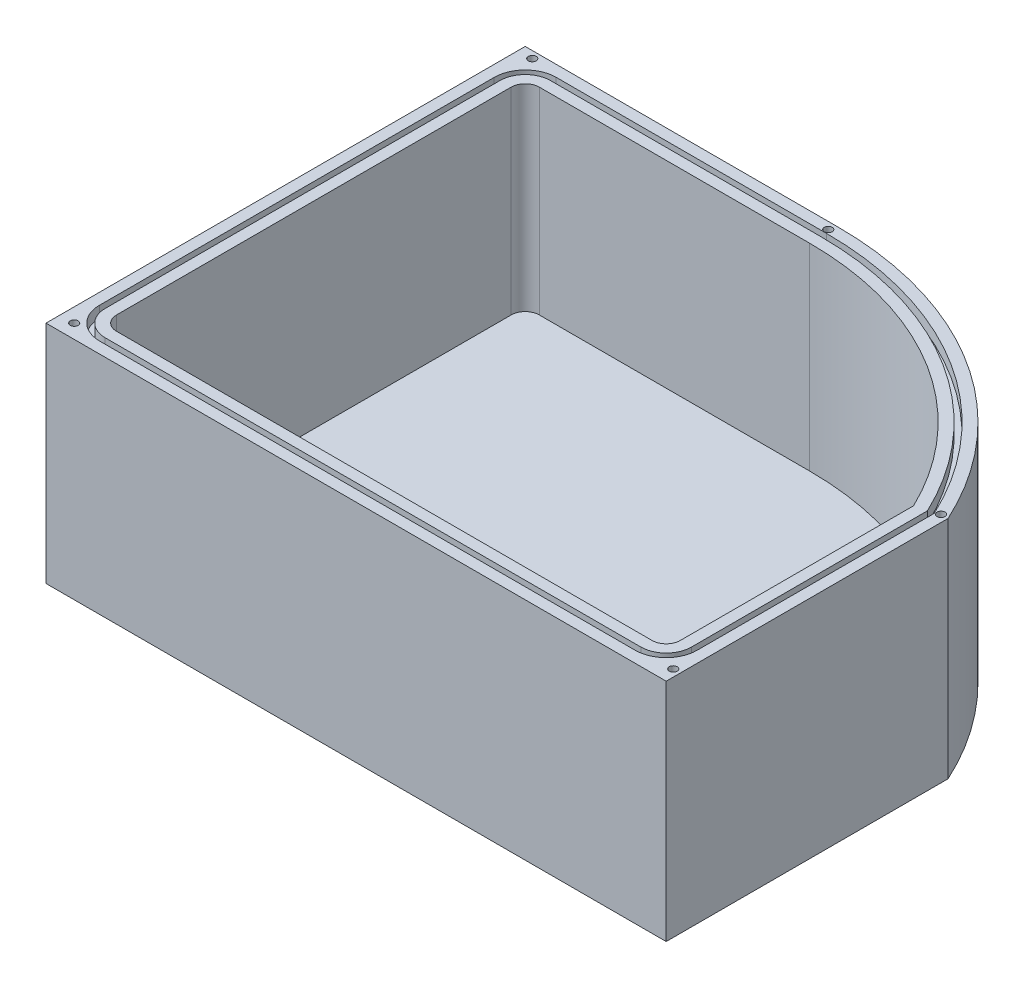
SolidWorks part; units mm, degrees
ref_plane "Front Plane" through (0, 0, 0) normal (0, 0, 1) x (1, 0, 0)
ref_plane "Top Plane" through (0, 0, 0) normal (0, 1, 0) x (1, 0, 0)
ref_plane "Right Plane" through (0, 0, 0) normal (1, 0, 0) x (0, 0, -1)
sketch "Sketch2" plane through (0, 0, 0) normal (0, 1, 0) x (1, 0, 0)
  line L0 (139.7, 63.5) -> (70.4297, 63.5) construction
  line L1 (0, 0) -> (139.7, 0)
  line L2 (0, 0) -> (0, 107.95)
  line L3 (0, 107.95) -> (70.4297, 107.95)
  line L4 (139.7, 0) -> (139.7, 63.5)
  line L5 (70.4297, 63.5) -> (70.4297, 107.95) construction
  arc A0 (70.4297, 107.95) -> (139.7, 63.5) centre (70.4297, 31.75) cw
  dimension "D4" = 76.2
  dimension "D1" = 107.95
  dimension "D2" = 139.7
  dimension "D3" = 63.5
extrude "Boss-Extrude1" add sketch "Sketch2" along normal blind 50.8
shell "Shell1" thickness 6.35
fillet "Fillet1" radius 3.175 3 edges at (133.35, 28.575, -6.35) (6.35, 28.575, -6.35) (6.35, 28.575, -101.6)
sketch "Sketch4" plane through (0, 50.8, 0) normal (0, 1, 0) x (1, 0, 0)
  line L20 (2.54, 98.425) -> (2.54, 9.525)
  line L21 (9.525, 2.54) -> (130.175, 2.54)
  line L22 (137.16, 9.525) -> (137.16, 62.9407)
  line L23 (70.4297, 105.41) -> (9.525, 105.41)
  line L24 (9.525, 3.81) -> (130.175, 3.81)
  line L25 (135.89, 9.525) -> (135.89, 62.6573)
  line L26 (70.4297, 104.14) -> (9.525, 104.14)
  line L27 (3.81, 98.425) -> (3.81, 9.525)
  line L28 (9.525, 3.81) -> (130.175, 3.81)
  line L29 (135.89, 9.525) -> (135.89, 62.6573)
  line L30 (70.4297, 104.14) -> (9.525, 104.14)
  line L31 (3.81, 98.425) -> (3.81, 9.525)
  arc A16 (9.525, 105.41) -> (2.54, 98.425) centre (9.525, 98.425) ccw
  arc A17 (2.54, 9.525) -> (9.525, 2.54) centre (9.525, 9.525) ccw
  arc A18 (130.175, 2.54) -> (137.16, 9.525) centre (130.175, 9.525) ccw
  arc A19 (137.16, 62.9407) -> (70.4297, 105.41) centre (70.4297, 31.75) ccw
  arc A20 (3.81, 9.525) -> (9.525, 3.81) centre (9.525, 9.525) ccw
  arc A21 (130.175, 3.81) -> (135.89, 9.525) centre (130.175, 9.525) ccw
  arc A22 (135.89, 62.6573) -> (70.4297, 104.14) centre (70.4297, 31.75) ccw
  arc A23 (9.525, 104.14) -> (3.81, 98.425) centre (9.525, 98.425) ccw
  arc A24 (3.81, 9.525) -> (9.525, 3.81) centre (9.525, 9.525) ccw
  arc A25 (130.175, 3.81) -> (135.89, 9.525) centre (130.175, 9.525) ccw
  arc A26 (135.89, 62.6573) -> (70.4297, 104.14) centre (70.4297, 31.75) ccw
  arc A27 (9.525, 104.14) -> (3.81, 98.425) centre (9.525, 98.425) ccw
  dimension "D1" = 2.54
  dimension "D2" = 1.27
extrude "Cut-Extrude1" cut sketch "Sketch4" against normal blind 2.54
sketch "Sketch5" plane through (0, 50.8, 0) normal (0, 1, 0) x (1, 0, 0)
  line L0 (0, 0) -> (139.7, 0) construction
  line L1 (0, 107.95) -> (0, 0) construction
  line L2 (70.4297, 107.95) -> (0, 107.95) construction
  line L3 (139.7, 0) -> (139.7, 63.5) construction
  point P0 (3.175, 3.175)
  point P2 (3.175, 106.3625)
  point P4 (69.85, 106.3625)
  point P6 (138.1125, 63.5)
  point P8 (138.1125, 3.175)
  point P10 (3.175, 106.3625)
  point P11 (0, 0)
  point P12 (0, 0)
  point P13 (0, 0)
  point P14 (0, 0)
  point P23 (0, 0)
  point P24 (0, 0)
  dimension "D1" = 3.175
  dimension "D2" = 3.175
  dimension "D3" = 3.175
  dimension "D4" = 1.5875
  dimension "D5" = 1.5875
  dimension "D6" = 3.175
  dimension "D7" = 60.325
  dimension "D8" = 66.675
  dimension "D9" = 103.1875
  dimension "D10" = 134.9375
hole_wizard "#2-64 Tapped Hole1" positions "Sketch5" profile "Sketch6" tap size "#2-64" standard "ANSI Inch"
sketch "Sketch6" plane through (3.175, 50.8, -3.175) normal (1, 0, 0) x (0, 0, 1)
  line L0 (0, 0) -> (0, 6.8842)
  line L1 (0, 6.8842) -> (0.889, 6.35)
  line L2 (0.889, 6.35) -> (0.889, 0)
  line L5 (0.889, 0) -> (0, 0)
  line L10 (0, 6.8842) -> (-0.889, 6.35) construction
  line L11 (0, -6.35) -> (0, 107.95) construction
  dimension "Tap Drill Dia." = 1.778
  dimension "Tap Drill Depth" = 6.35
  dimension "Drill Angle" = 118
cosmetic thread "Hole Thread1" parameters "D1"=5.9538, "D2"=2.1844
cosmetic thread "Hole Thread2" parameters "D1"=5.9538, "D2"=2.1844
cosmetic thread "Hole Thread3" parameters "D1"=5.9538, "D2"=2.1844
cosmetic thread "Hole Thread4" parameters "D1"=5.9538, "D2"=2.1844
cosmetic thread "Hole Thread5" parameters "D1"=5.9538, "D2"=2.1844
cosmetic thread "Hole Thread6" parameters "D1"=5.9538, "D2"=2.1844
